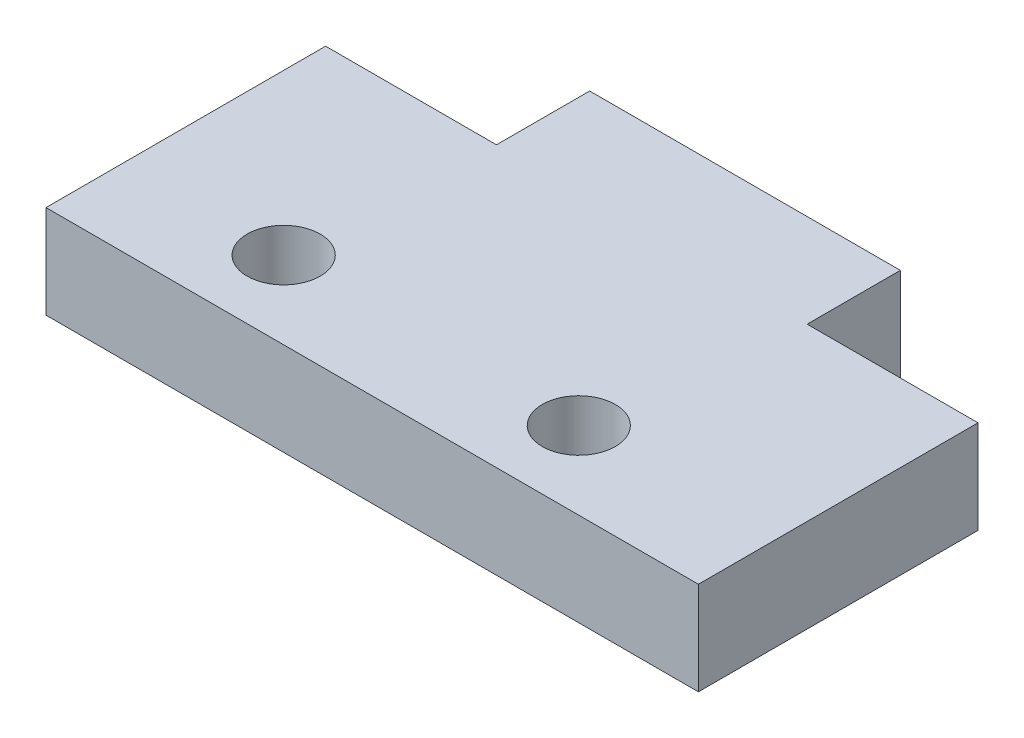
SolidWorks part; units mm, degrees
ref_plane "Alzado" through (0, 0, 0) normal (0, 0, 1) x (1, 0, 0)
ref_plane "Planta" through (0, 0, 0) normal (0, 1, 0) x (1, 0, 0)
ref_plane "Vista lateral" through (0, 0, 0) normal (1, 0, 0) x (0, 0, -1)
sketch "Croquis1" plane through (0, 0, 0) normal (0, 1, 0) x (1, 0, 0)
  line L0 (0, 0) -> (10, 0)
  line L1 (10, 0) -> (10, -3)
  line L2 (10, -3) -> (15.5, -3)
  line L3 (15.5, -3) -> (15.5, -12)
  line L4 (15.5, -12) -> (-5.5, -12)
  line L5 (-5.5, -12) -> (-5.5, -3)
  line L6 (-5.5, -3) -> (0, -3)
  line L7 (0, -3) -> (0, 0)
  line L8 (14, -3) -> (14, -12) construction
  circle A0 centre (-0.35, -9.5) radius 1.175
  circle A1 centre (9.15, -9.5) radius 1.175
  dimension "D7" = 2.35
  dimension "D8" = 2.35
  dimension "D1" = 10
  dimension "D2" = 3
  dimension "D3" = 12
  dimension "D4" = 21
  dimension "D5" = 5.5
  dimension "D6" = 19.5
  dimension "D9" = 2.5
  dimension "D10" = 2.5
  dimension "D11" = 5.15
  dimension "D12" = 9.5
extrude "Saliente-Extruir1" add sketch "Croquis1" along normal blind 3
